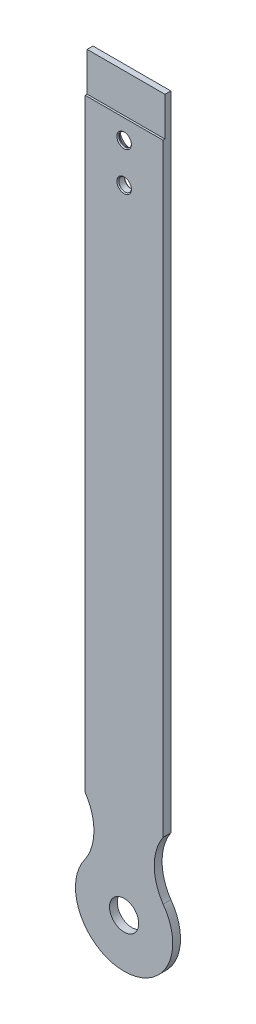
SolidWorks part; units mm, degrees
ref_plane "Спереди" through (0, 0, 0) normal (0, 0, 1) x (1, 0, 0)
ref_plane "Сверху" through (0, 0, 0) normal (0, 1, 0) x (1, 0, 0)
ref_plane "Справа" through (0, 0, 0) normal (1, 0, 0) x (0, 0, -1)
sketch "Эскиз1" plane through (0, 0, 0) normal (0, 0, 1) x (1, 0, 0)
  line L0 (20, 69.629) -> (20, 400)
  line L1 (20, 400) -> (-20, 400)
  line L2 (0, 481.0809) -> (0, -73.6647) construction
  line L3 (-20, 69.629) -> (-20, 400)
  arc A0 (-20.0599, 39.9199) -> (20.0599, 39.9199) centre (0, 25) ccw
  arc A1 (20.0599, 39.9199) -> (20, 69.629) centre (42.1304, 54.819) cw
  arc A2 (-20.0599, 39.9199) -> (-20, 69.629) centre (-42.1304, 54.819) ccw
  circle A3 centre (0, 370) radius 3.25
  circle A4 centre (0, 350) radius 3.25
  circle A5 centre (0, 25) radius 7.5
  point P13 (0, 400)
  point P15 (0, 0)
  point P17 (0, 0)
extrude "Бобышка-Вытянуть1" add sketch "Эскиз1" along normal blind 4
sketch "Эскиз2" plane through (-20, 0, 0) normal (-1, 0, 0) x (0, 0, 1)
  line L0 (3, 400) -> (3, 380.0564)
  line L1 (4, 400) -> (0, 400) construction
  line L2 (3, 380.0564) -> (4, 380.0564)
  line L3 (4, 400) -> (4, 69.629) construction
  line L4 (4, 380.0564) -> (4, 400)
  line L5 (4, 400) -> (3, 400)
extrude "Вырез-Вытянуть1" cut sketch "Эскиз2" against normal through all
chamfer "Фаска1" distance 3 angle 45 1 edges at (3.25, 370, 0)
chamfer "Фаска2" distance 0.5 angle 45 3 edges at (3.25, 350, 0) (3.25, 350, 4) (3.25, 370, 4)
